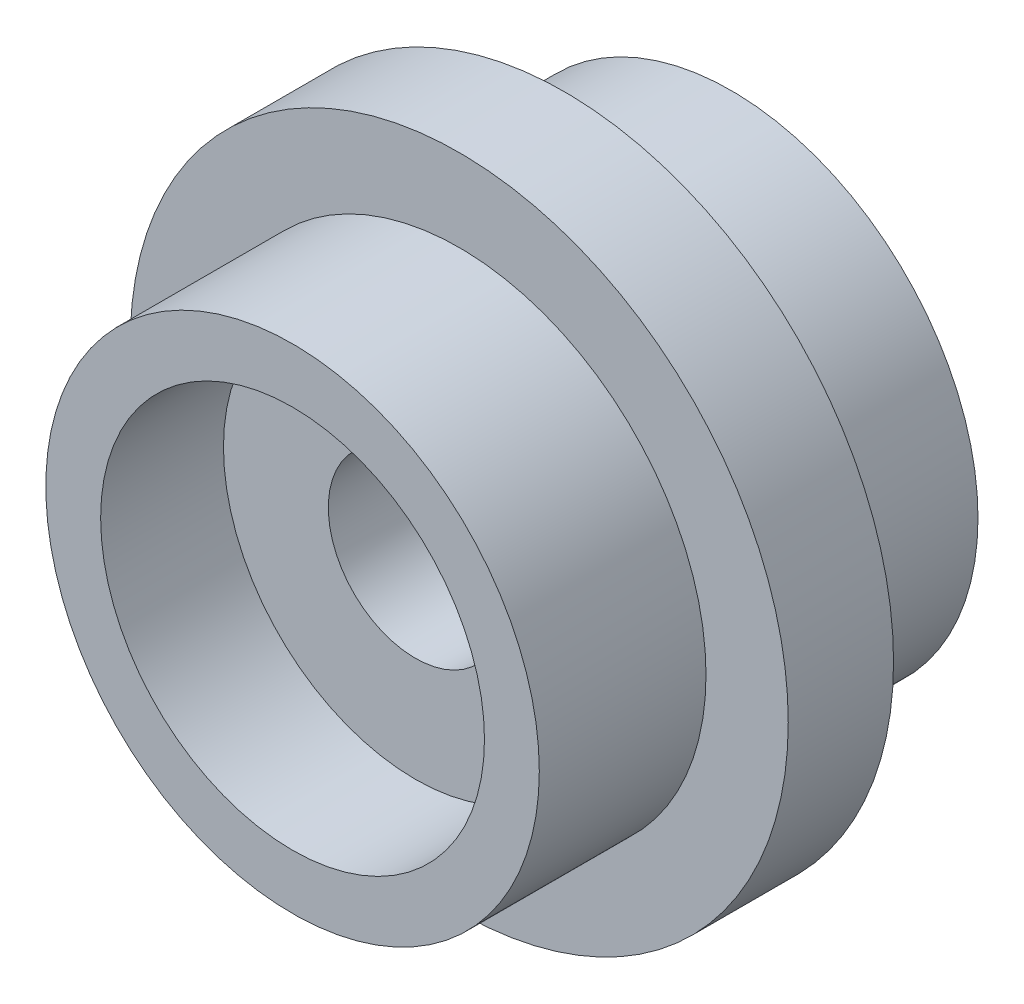
SolidWorks part; units mm, degrees
ref_plane "Front Plane" through (0, 0, 0) normal (0, 0, 1) x (1, 0, 0)
ref_plane "Top Plane" through (0, 0, 0) normal (0, 1, 0) x (1, 0, 0)
ref_plane "Right Plane" through (0, 0, 0) normal (1, 0, 0) x (0, 0, -1)
sketch "Sketch1" plane through (0, 0, 0) normal (1, 0, 0) x (0, 0, -1)
  line L0 (-13.6967, 0) -> (33.3737, 0) construction
  line L1 (0, 0) -> (0, 14.2875)
  line L2 (0, 14.2875) -> (9.652, 14.2875)
  line L3 (25.4, 14.2875) -> (25.4, 0)
  line L4 (25.4, 0) -> (0, 0)
  line L5 (9.652, 14.2875) -> (9.652, 19.05)
  line L6 (9.652, 19.05) -> (15.748, 19.05)
  line L7 (15.748, 19.05) -> (15.748, 14.2875)
  line L8 (15.748, 14.2875) -> (25.4, 14.2875)
  point P9 (12.7, 0)
  point P12 (12.7, 19.05)
  dimension "D1" = 14.2875
  dimension "D2" = 25.4
  dimension "D3" = 6.096
  dimension "D4" = 19.05
revolve "Revolve1" add sketch "Sketch1" angle 360 about L0
hole_wizard "3/8 Clearance Hole1" positions "Sketch2" profile "Sketch3" hole size "3/8" standard "ANSI Inch" end condition up to next
sketch "Sketch2" plane through (0, 0, 0) normal (0, 0, 1) x (1, 0, 0)
  point P0 (0, 0)
sketch "Sketch3" plane through (0, 0, 0) normal (1, 0, 0) x (0, -1, 0)
  line L0 (0, 0) -> (0, 25.4)
  line L1 (0, 25.4) -> (5.0419, 25.4)
  line L2 (5.0419, 25.4) -> (5.0419, 0)
  line L5 (5.0419, 0) -> (0, 0)
  line L11 (0, -6.35) -> (0, 107.95) construction
  dimension "Thru Hole Dia." = 10.0838
  dimension "Thru Hole Depth" = 25.4
sketch "Sketch6" plane through (0, 0, 0) normal (0, 0, 1) x (1, 0, 0)
  circle A0 centre (0, 0) radius 11.1125
  dimension "D1" = 22.225
extrude "Cut-Extrude1" cut sketch "Sketch6" against normal blind 7.112
sketch "Sketch7" plane through (0, 0, -25.4) normal (0, 0, -1) x (-1, 0, 0)
  circle A0 centre (0, 0) radius 11.1125
  dimension "D1" = 22.225
extrude "Cut-Extrude2" cut sketch "Sketch7" against normal blind 12.065
